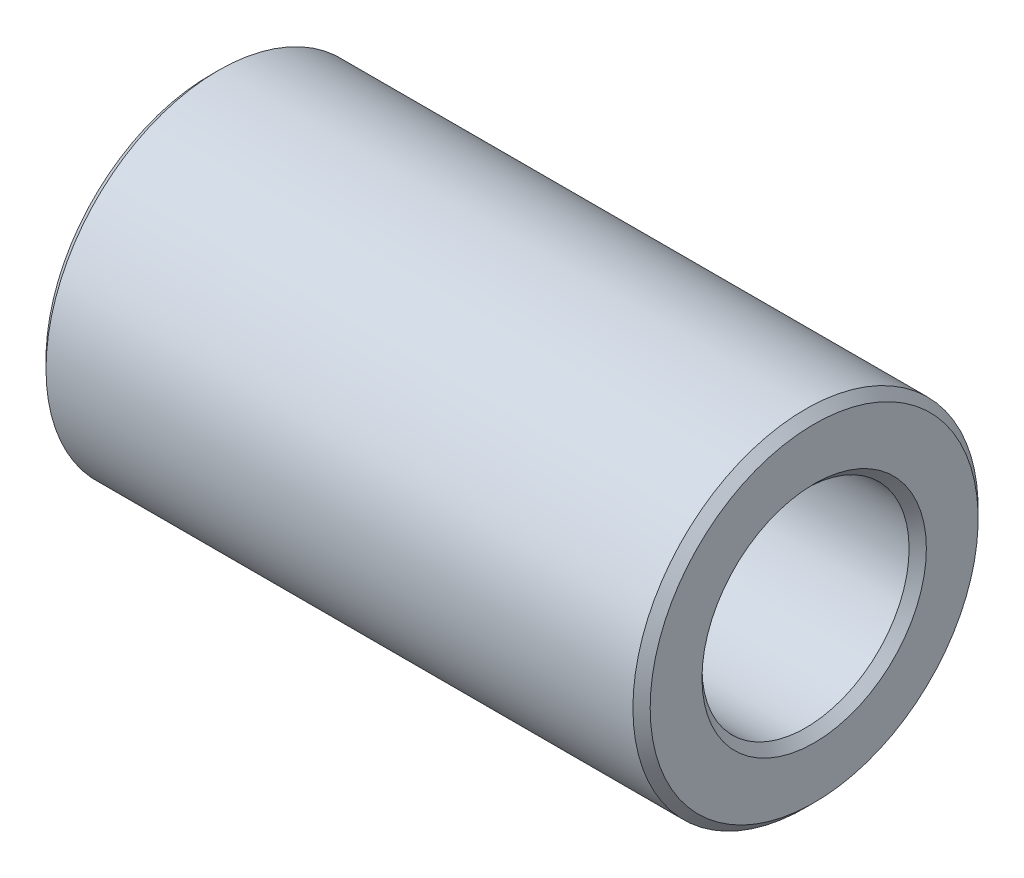
SolidWorks part; units mm, degrees
ref_plane "Front Plane" through (0, 0, 0) normal (0, 0, 1) x (1, 0, 0)
ref_plane "Top Plane" through (0, 0, 0) normal (0, 1, 0) x (1, 0, 0)
ref_plane "Right Plane" through (0, 0, 0) normal (1, 0, 0) x (0, 0, -1)
sketch "Sketch1" plane through (0, 0, 0) normal (0, 0, 1) x (1, 0, 0)
  line L0 (0, 6) -> (35, 6)
  line L1 (0, 10) -> (35, 10)
  line L2 (0, 6) -> (0, 10)
  line L3 (35, 6) -> (35, 10)
  line L4 (-1000, 0) -> (49000, 0) construction
  dimension "D1" = 10
  dimension "D2" = 6
  dimension "D3" = 35
  dimension "D4" = 35
  dimension "D5" = 4
revolve "Revolve1" add sketch "Sketch1" angle 360 about L4
chamfer "Chamfer1" distance 0.5 angle 45 4 edges at (35, 0, 10) (35, 0, 6) (0, 0, 6) (0, 0, 10)
